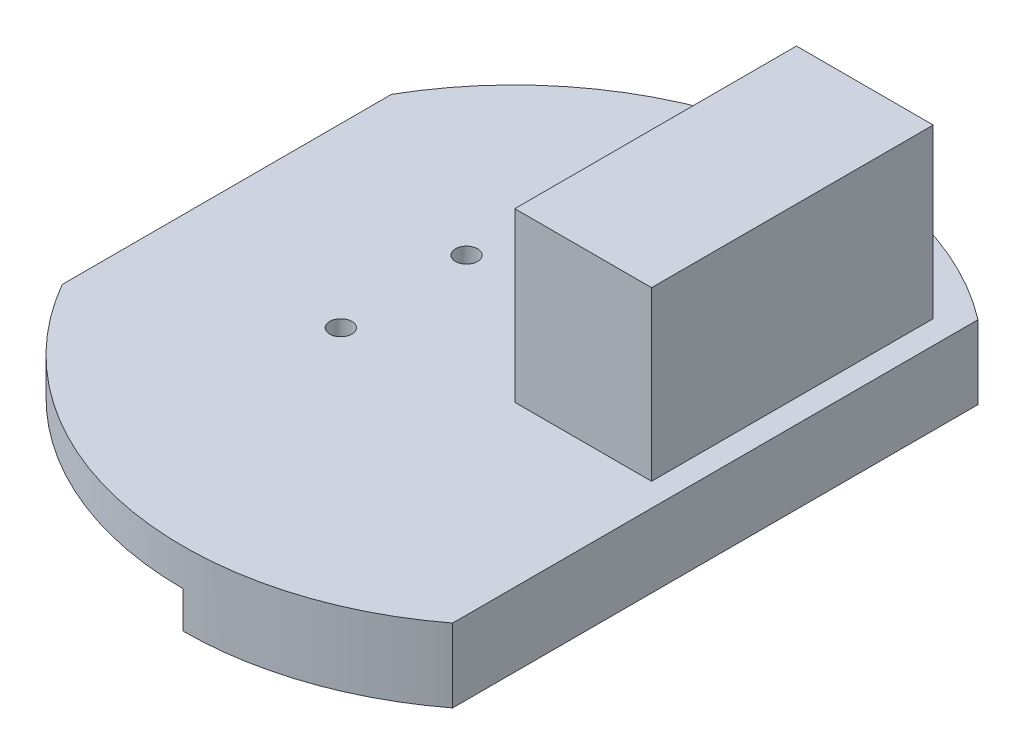
SolidWorks part; units mm, degrees
material "A-玻璃纤维"
ref_plane "前视基准面" through (0, 0, 0) normal (0, 0, 1) x (1, 0, 0)
ref_plane "上视基准面" through (0, 0, 0) normal (0, 1, 0) x (1, 0, 0)
ref_plane "右视基准面" through (0, 0, 0) normal (1, 0, 0) x (0, 0, -1)
sketch "草图1" plane through (0, 0, 0) normal (0, 1, 0) x (1, 0, 0)
  line L0 (-39.0386, -22.3828) -> (-39.0386, 22.3828)
  line L5 (-23.181, 22.3828) -> (23.181, -22.3828) construction
  line L6 (-23.181, -22.3828) -> (23.181, 22.3828) construction
  line L7 (-15, -8.55) -> (15, -8.55)
  line L8 (-15, -8.55) -> (-15, -7.05)
  line L9 (-15, 8.55) -> (15, 8.55)
  line L10 (15, -8.55) -> (15, 8.55)
  line L11 (-15, -8.55) -> (15, 8.55) construction
  line L12 (-15, 8.55) -> (15, -8.55) construction
  line L13 (27.3745, -35.716) -> (27.3745, 35.716)
  line L14 (-15, 7.05) -> (-15, 8.55)
  circle A0 centre (-15, 8.55) radius 1.5
  circle A1 centre (-15, -8.55) radius 1.5
  circle A3 centre (15, 8.55) radius 3
  arc A4 (-39.0386, -22.3828) -> (27.3745, -35.716) centre (0, 0) ccw
  arc A5 (27.3745, 35.716) -> (-39.0386, 22.3828) centre (0, 0) ccw
  circle A6 centre (15, 8.55) radius 3
  point P0 (0, 0)
  point P6 (0, 0)
  dimension "D3" = 3
  dimension "D4" = 6
  dimension "D5" = 3
  dimension "D1" = 17.1
  dimension "D2" = 30
extrude "凸台-拉伸1" add sketch "草图1" along normal blind 5
sketch "草图3" plane through (0, 5, 0) normal (0, 1, 0) x (1, 0, 0)
  line L0 (27.3745, 9.8315) -> (21.2045, 9.8315) construction
  line L1 (27.3745, -35.716) -> (27.3745, 35.716) construction
  line L2 (14.9045, -2.5) -> (14.9045, 29.8) construction
  line L3 (21.2045, -2.5) -> (8.6045, -2.5)
  line L4 (21.2045, -2.5) -> (21.2045, 29.8)
  line L5 (21.2045, 29.8) -> (8.6045, 29.8)
  line L6 (8.6045, -2.5) -> (8.6045, 29.8)
  line L8 (24.2045, -5.5) -> (5.6045, -5.5)
  line L9 (24.2045, -5.5) -> (24.2045, 32.8)
  line L10 (24.2045, 32.8) -> (5.6045, 32.8)
  line L11 (5.6045, -5.5) -> (5.6045, 32.8)
  line L12 (24.2045, -5.5) -> (5.6045, 32.8) construction
  line L13 (24.2045, 32.8) -> (5.6045, -5.5) construction
  circle A1 centre (-15, 8.55) radius 1.5 construction
  point P10 (14.9045, 13.65)
  dimension "D5" = 21.25
  dimension "D1" = 32.3
  dimension "D2" = 12.6
  dimension "D3" = 3
  dimension "D4" = 3
extrude "凸台-拉伸3" add sketch "草图3" along normal mid plane 39.6
sketch "草图4" plane through (0, 24.8, 0) normal (0, 1, 0) x (1, 0, 0)
  line L1 (24.2045, -5.5) -> (5.6045, -5.5)
  line L2 (24.2045, -5.5) -> (24.2045, 32.8)
  line L3 (24.2045, 32.8) -> (5.6045, 32.8)
  line L4 (5.6045, -5.5) -> (5.6045, 32.8)
extrude "凸台-拉伸4" add sketch "草图4" along normal blind 3
sketch "草图7" plane through (0, 0, 0) normal (0, -1, 0) x (-1, 0, 0)
  line L1 (-8.6045, 29.8) -> (-21.2045, 29.8)
  line L2 (-8.6045, 29.8) -> (-8.6045, -2.5)
  line L3 (-8.6045, -2.5) -> (-21.2045, -2.5)
  line L4 (-21.2045, 29.8) -> (-21.2045, -2.5)
extrude "切除-拉伸1" cut sketch "草图7" against normal up to surface (5 mm away) up to face at (-7.3448, 5, 0)
sketch "草图8" plane through (0, -14.8, 0) normal (0, -1, 0) x (-1, 0, 0)
  line L1 (4.2196, 43.7537) -> (-31.7079, 43.7537)
  line L2 (4.2196, 43.7537) -> (4.2196, -9.4804)
  line L3 (4.2196, -9.4804) -> (-31.7079, -9.4804)
  line L4 (-31.7079, 43.7537) -> (-31.7079, -9.4804)
extrude "切除-拉伸2" cut sketch "草图8" against normal up to surface (14.8 mm away) up to face at (-7.3448, 0, 0)
sketch "草图9" plane through (0, 24.8, 0) normal (0, -1, 0) x (1, 0, 0)
  line L0 (21.2045, 2.5) -> (21.2045, -29.8) construction
  line L1 (8.6045, -29.8) -> (21.2045, -29.8)
  line L2 (8.6045, -29.8) -> (8.6045, -25.1)
  line L3 (8.6045, -25.1) -> (21.2045, -25.1)
  line L4 (21.2045, -29.8) -> (21.2045, -25.1)
  dimension "D1" = 4.7
extrude "凸台-拉伸5" add sketch "草图9" along normal blind 15.2
sketch "草图10" plane through (0, 9.6, 0) normal (0, -1, 0) x (-1, 0, 0)
  line L0 (-8.6045, 29.8) -> (-21.2045, 29.8) construction
  line L1 (-14.9045, 29.8) -> (-14.9045, 25.4507) construction
  circle A0 centre (-14.9045, 27.9) radius 1.1
  dimension "D1" = 1.9
extrude "切除-拉伸3" cut sketch "草图10" against normal blind 10
ref_plane "基准面1" through (0, 0, -13.65) normal (0, 0, 1) x (1, 0, 0)
mirror "镜向1" about plane through (0, 0, -13.65) normal (0, 0, 1) of "切除-拉伸3", "凸台-拉伸5"
sketch "草图11" plane through (0, 0, 0) normal (0, -1, 0) x (-1, 0, 0)
  line L0 (0, 45) -> (0, -45)
  line L1 (-25.3745, 37.1636) -> (-25.3745, -37.1636)
  line L2 (-27.3745, -35.716) -> (-27.3745, 35.716) construction
  line L3 (-27.3745, 35.716) -> (-27.3745, -35.716)
  circle A0 centre (0, 0) radius 42
  circle A1 centre (0, 0) radius 45
  line M5 (-27.3745, 35.716) -> (-27.3745, -35.716)
  dimension "D1" = 2
extrude "凸台-拉伸6" add sketch "草图11" along normal blind 5 contours L1 A1 L0 A0 | A1 L1 A0 M5 | L3 A0 L1 | L1 A1 L3 A0 | L0 A1 L1 A0
ref_plane "基准面2" through (0, -5, -42) normal (1, 0, 0) x (0, 0, -1)
sketch "草图13" plane through (0, -5, 0) normal (0, -1, 0) x (-1, 0, 0)
  line L0 (-27.3745, 35.716) -> (-27.3745, -35.716) construction
  circle A0 centre (0, 0) radius 43.5
  circle A1 centre (-5.0745, 43.203) radius 1
  circle A2 centre (-26.0745, 34.8191) radius 1
  circle A3 centre (-26.0745, -34.8191) radius 1
  circle A4 centre (-5.0745, -43.203) radius 1
  dimension "D1" = 1.3
  dimension "D2" = 22.3
  dimension "D3" = 2
  dimension "D4" = 2
  dimension "D5" = 1.3
  dimension "D6" = 2
  dimension "D7" = 22.3
  dimension "D8" = 87
  dimension "D9" = 2
extrude "切除-拉伸4" cut sketch "草图13" against normal blind 5 contours A0 A4 | A0 A4 | A0 A3 | A0 A3 | A0 A2 | A0 A2 | A0 A1 | A0 A1
